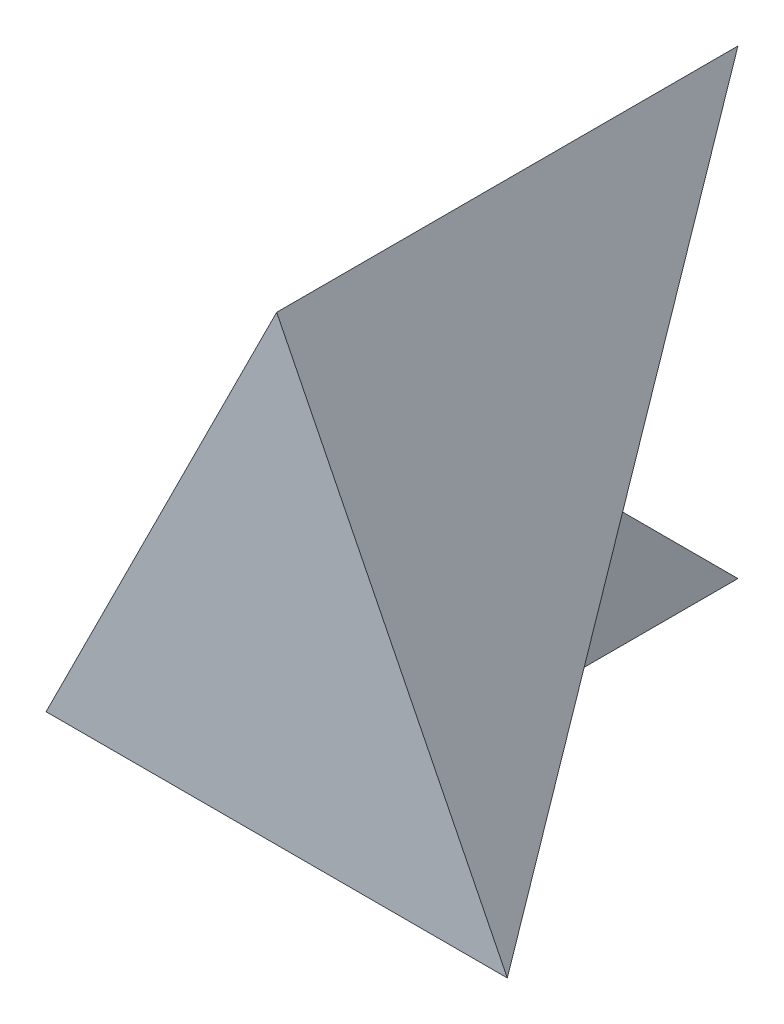
SolidWorks part; units mm, degrees
ref_plane "Front" through (0, 0, 0) normal (0, 0, 1) x (1, 0, 0)
ref_plane "Top" through (0, 0, 0) normal (0, 1, 0) x (1, 0, 0)
ref_plane "Right" through (0, 0, 0) normal (1, 0, 0) x (0, 0, -1)
sketch "Sketch1" plane through (0, 0, 0) normal (0, 1, 0) x (1, 0, 0)
  line L1 (-2, -2) -> (2, -2)
  line L2 (-2, -2) -> (-2, 2)
  line L3 (-2, 2) -> (2, 2)
  line L4 (2, -2) -> (2, 2)
  line L5 (-2, -2) -> (2, 2) construction
  line L6 (-2, 2) -> (2, -2) construction
  point P0 (0, 0)
  dimension "D1" = 4
  dimension "D2" = 4
extrude "Boss-Extrude1" add sketch "Sketch1" along normal blind 4
sketch "Sketch2" plane through (-2, 0, 0) normal (-1, 0, 0) x (0, 0, 1)
  line L0 (2, 4) -> (-2, 0)
  line L1 (-2, 0) -> (-2, 4)
  line L2 (-2, 4) -> (2, 4)
extrude "Cut-Extrude1" cut sketch "Sketch2" against normal blind 2
sketch "Sketch3" plane through (2, 0, 0) normal (1, 0, 0) x (0, 0, -1)
  line L0 (-2, 0) -> (2, 4)
  line L1 (2, 4) -> (-2, 4)
  line L2 (-2, 4) -> (-2, 0)
  line M4 (-2, 0) -> (2, 0)
  line M5 (2, 0) -> (2, 4)
extrude "Cut-Extrude2" cut sketch "Sketch3" against normal blind 2 contours L0 M4 M5
sketch "Sketch4" plane through (0, 0, 2) normal (0, 0, 1) x (1, 0, 0)
  line L0 (2, 0) -> (0, 4)
  line L1 (0, 4) -> (-2, 0)
  line L7 (2, 0) -> (2, 4)
  line L8 (0, 0) -> (2, 0)
  line L9 (0, 2) -> (0, 0)
  line L10 (0, 4) -> (0, 2)
  line L11 (2, 4) -> (0, 4)
  line L12 (2, 0) -> (2, 4)
  line L13 (0, 0) -> (2, 0)
  line L14 (0, 2) -> (0, 0)
  line L15 (0, 4) -> (0, 2)
  line L16 (2, 4) -> (0, 4)
  line L17 (-2, 4) -> (-2, 0)
  line L18 (0, 4) -> (-2, 4)
  line L19 (0, 2) -> (0, 4)
  line L20 (0, 0) -> (0, 2)
  line L21 (-2, 0) -> (0, 0)
  line L22 (-2, 4) -> (-2, 0)
  line L23 (0, 4) -> (-2, 4)
  line L24 (0, 2) -> (0, 4)
  line L25 (0, 0) -> (0, 2)
  line L26 (-2, 0) -> (0, 0)
  line M13 (2, 0) -> (2, 4)
  line M14 (2, 4) -> (0, 4)
  dimension "D1" = 0
  dimension "D2" = 0
extrude "Cut-Extrude3" cut sketch "Sketch4" against normal blind 10 contours L0 M13 M14
sketch3d "3DSketch1"
  line L0 (0, 0, -2) -> (-2, 0, 2)
  line L1 (-2, 0, 2) -> (0, 4, 2)
  line L2 (0, 4, 2) -> (0, 0, -2)
extrude "Cut-Extrude4" cut sketch "3DSketch1" along direction (0, 0, -1) on the side against the normal blind 10
